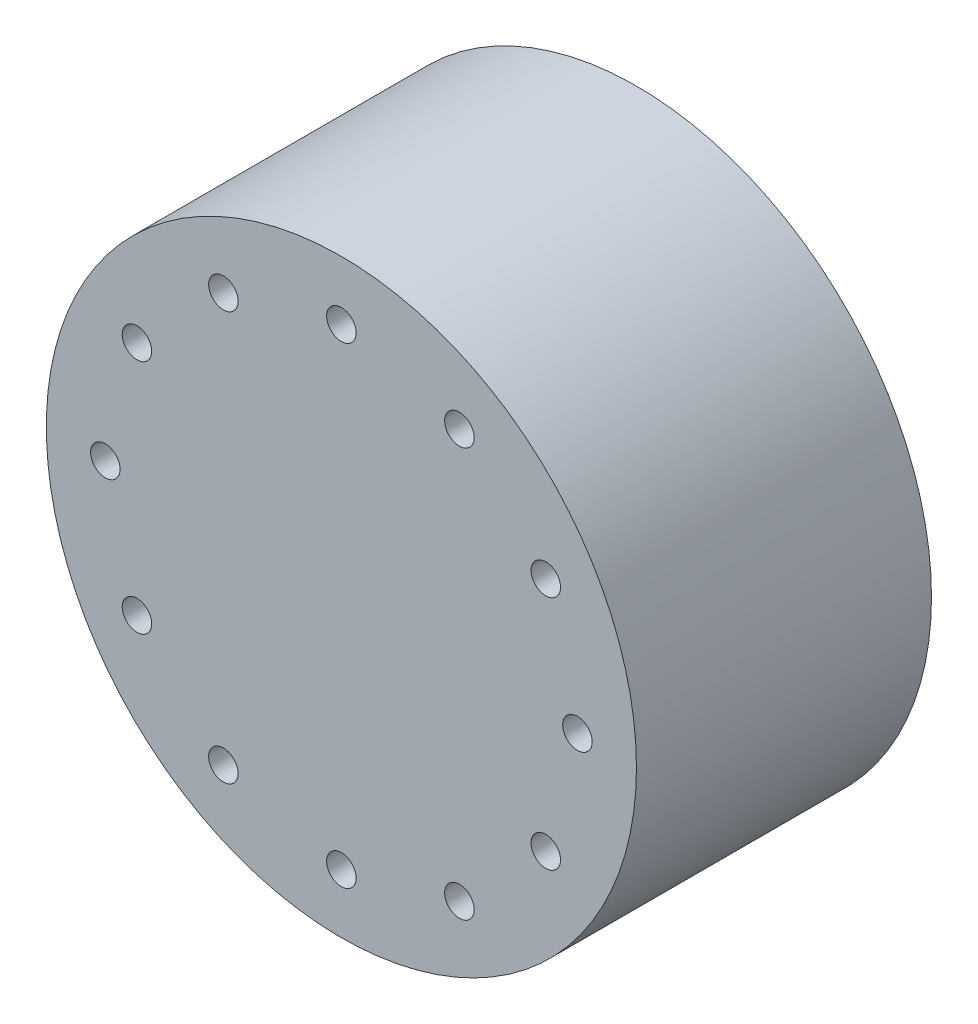
SolidWorks part; units mm, degrees
ref_plane "Front Plane" through (0, 0, 0) normal (0, 0, 1) x (1, 0, 0)
ref_plane "Top Plane" through (0, 0, 0) normal (0, 1, 0) x (1, 0, 0)
ref_plane "Right Plane" through (0, 0, 0) normal (1, 0, 0) x (0, 0, -1)
sketch "Sketch1" plane through (0, 0, 0) normal (0, 0, 1) x (1, 0, 0)
  circle A0 centre (0, 0) radius 5
  dimension "D1" = 10
extrude "Boss-Extrude1" add sketch "Sketch1" along normal blind 5
sketch "Sketch2" plane through (0, 0, 5) normal (0, 0, 1) x (1, 0, 0)
  circle A0 centre (4, 0) radius 0.25
  dimension "D1" = 0.5
  dimension "D2" = 4
extrude "Cut-Extrude1" cut sketch "Sketch2" against normal through all
pattern_circular "CirPattern1" count 12 over 360 about axis through (0, 0, 0) along (0, 0, 1) of "Cut-Extrude1"
